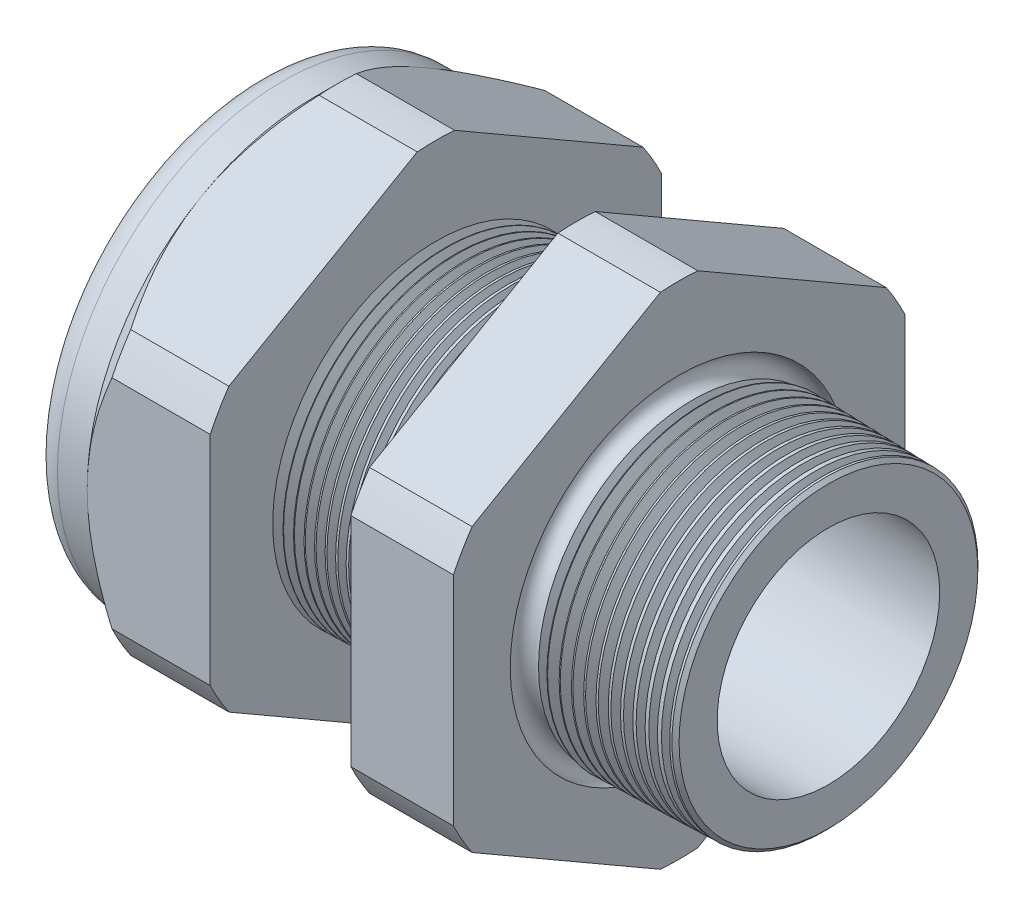
SolidWorks part; units mm, degrees
ref_plane "Front Plane" through (0, 0, 0) normal (0, 0, 1) x (1, 0, 0)
ref_plane "Top Plane" through (0, 0, 0) normal (0, 1, 0) x (1, 0, 0)
ref_plane "Right Plane" through (0, 0, 0) normal (1, 0, 0) x (0, 0, -1)
sketch "Sketch10" plane through (0, 0, 0) normal (0, 0, 1) x (1, 0, 0)
  line L0 (0, 0) -> (-115.3565, 0) construction
  line L1 (-38.862, 9.017) -> (-25.662, 9.017)
  line L2 (3.048, 8.1382) -> (3.048, 11.1862)
  line L3 (-7.874, 11.4722) -> (3.048, 11.1862)
  line L4 (-7.874, 33.02) -> (-7.874, 11.4722)
  line L5 (-7.874, 33.02) -> (-15.374, 33.02)
  line L6 (-15.374, 33.02) -> (-15.374, 11.6686)
  line L7 (-25.662, 11.938) -> (-15.374, 11.6686)
  line L8 (-25.662, 11.938) -> (-25.662, 33.02)
  line L9 (-25.662, 33.02) -> (-34.662, 33.02)
  line L10 (-34.662, 33.02) -> (-34.662, 16.51)
  line L11 (-34.662, 16.51) -> (-38.862, 16.51)
  line L12 (-38.862, 16.51) -> (-38.862, 9.017)
  line L13 (-25.662, 9.017) -> (3.048, 8.1382)
  dimension "D1" = 41.91
  dimension "D2" = 18.034
  dimension "D3" = 1.5
  dimension "D4" = 3.048
  dimension "A" = 23.876
  dimension "D6" = 33.02
  dimension "D8" = 66.04
  dimension "D9" = 4.2
  dimension "D10" = 9
  dimension "D11" = 7.5
  dimension "D" = 10.922
revolve "Revolve2" add sketch "Sketch10" angle 360 about L0
sketch "Sketch12" plane through (-34.662, 0, 0) normal (-1, 0, 0) x (0, 0, 1)
  line L1 (-1.3666, 18.2751) -> (-15.1434, 10.3211)
  line L2 (-16.51, 7.954) -> (-16.51, -7.954)
  line L3 (-15.1434, -10.3211) -> (-1.3666, -18.2751)
  line L4 (1.3666, -18.2751) -> (15.1434, -10.3211)
  line L5 (16.51, -7.954) -> (16.51, 7.954)
  line L6 (15.1434, 10.3211) -> (1.3666, 18.2751)
  circle A0 centre (0, 0) radius 16.51 construction
  arc A1 (1.3666, 18.2751) -> (-1.3666, 18.2751) centre (0, 0) ccw
  arc A2 (-15.1434, 10.3211) -> (-16.51, 7.954) centre (0, 0) ccw
  arc A3 (-16.51, -7.954) -> (-15.1434, -10.3211) centre (0, 0) ccw
  arc A4 (-1.3666, -18.2751) -> (1.3666, -18.2751) centre (0, 0) ccw
  arc A5 (15.1434, -10.3211) -> (16.51, -7.954) centre (0, 0) ccw
  arc A6 (16.51, 7.954) -> (15.1434, 10.3211) centre (0, 0) ccw
  dimension "D2" = 36.6522
  dimension "D1" = 33.02
extrude "Cut-Extrude2" cut sketch "Sketch12" against normal through all flip side to cut
fillet "Fillet4" radius 2.032 1 edges at (-38.862, 0, -16.51)
sketch "Sketch19" plane through (-34.662, 0, 0) normal (-1, 0, 0) x (0, 0, 1)
  line L0 (16.51, 0) -> (16.51, 7.954) construction
  circle A0 centre (0, 0) radius 16.51
extrude "Cut-Extrude3" cut sketch "Sketch19" against normal blind 3.998 draft 45 flip side to cut
chamfer "Chamfer1" distance 0.254 angle 45 1 edges at (3.048, 0, -11.1862)
sketch "Sketch21" plane through (-38.862, 0, 0) normal (-1, 0, 0) x (0, 0, 1)
  circle A0 centre (0, 0) radius 9.017
  circle A2 centre (0, 0) radius 9.017 construction
extrude "plug" add sketch "Sketch21" against normal blind 8.89 separate body
sketch "Sketch22" plane through (-38.862, 0, 0) normal (-1, 0, 0) x (0, 0, 1)
  circle A0 centre (0, 0) radius 8.763
  circle A1 centre (0, 0) radius 9.017 construction
  dimension "D1" = 0.254
extrude "Cut-Extrude4" cut sketch "Sketch22" against normal blind 0.508
sketch "Sketch27" plane through (-38.354, 0, 0) normal (-1, 0, 0) x (0, 0, 1)
  line L0 (-4.3624, 0) -> (4.3624, 0) construction
  circle A0 centre (-4.8103, 0) radius 3.937
  circle A1 centre (0, 0) radius 8.763 construction
  dimension "D1" = 0.0157
  dimension "holedia" = 7.874
extrude "plugholes" cut sketch "Sketch27" against normal through all
pattern_circular "CirPattern1" count 2 over 360 about axis through (0, 0, 0) along (1, 0, 0) of "plugholes"
sketch "Sketch28" [suppressed] plane through (-29.464, 0, 0) normal (-1, 0, 0) x (0, 0, 1)
  circle A0 centre (0, 0) radius 0.762
  dimension "midholedia" = 7.874
extrude "midhole" [suppressed] cut sketch "Sketch28" against normal through all
sketch "Sketch29" plane through (0, 0, 0) normal (0, 0, 1) x (1, 0, 0)
  line L0 (-25.662, 11.938) -> (-24.929, 11.9188)
  line L1 (-15.374, 11.6686) -> (-25.662, 11.938) construction
  line L2 (-24.929, 11.9188) -> (-25.3121, 11.2936)
  line L3 (-25.3121, 11.2936) -> (-25.662, 11.938)
  dimension "D1" = 60
  dimension "D2" = 60
  dimension "D3" = 0.635
revolve "Cut-Revolve1" cut sketch "Sketch29" angle 360 about axis through (0, 0, 0) along (-1, 0, 0)
pattern_linear "LPattern1" count 14 spacing 0.762 along (1, 0, 0) of "Cut-Revolve1"
sketch "Sketch30" plane through (0, 0, 0) normal (0, 0, 1) x (1, 0, 0)
  line L0 (-7.874, 11.4722) -> (-6.9944, 11.4492)
  line L1 (-7.874, 18.2751) -> (-7.874, 10.3211) construction
  line L2 (2.7941, 11.1929) -> (-7.874, 11.4722) construction
  line L3 (-6.9944, 11.4492) -> (-7.4542, 10.6989)
  line L4 (-7.4542, 10.6989) -> (-7.874, 11.4722)
  dimension "D1" = 60
  dimension "D2" = 60
  dimension "D3" = 0.762
revolve "Cut-Revolve2" cut sketch "Sketch30" angle 360 about axis through (0, 0, 0) along (-1, 0, 0)
pattern_linear "LPattern2" count 12 spacing 0.889 along (1, 0, 0) of "Cut-Revolve2"
sketch "Sketch31" [suppressed] plane through (-38.354, 0, 0) normal (-1, 0, 0) x (0, 0, 1)
  line L0 (-1.905, 1.905) -> (1.905, 1.905)
  line L1 (-1.905, -1.905) -> (1.905, -1.905)
  circle A0 centre (0, 0) radius 1.905 construction
  arc A1 (-1.905, 1.905) -> (-1.905, -1.905) centre (-1.905, 0) ccw
  arc A2 (1.905, 1.905) -> (1.905, -1.905) centre (1.905, 0) cw
extrude "Cut-Extrude5" [suppressed] cut sketch "Sketch31" against normal through all
sketch "Sketch32" plane through (0, 0, 0) normal (0, 0, 1) x (1, 0, 0)
  line L0 (-7.874, 18.2751) -> (-7.874, 10.3211) construction
  circle A0 centre (-7.747, 11.4722) radius 0.889
  dimension "D2" = 1.778
  dimension "D1" = 0.127
revolve "Cut-Revolve3" cut sketch "Sketch32" angle 360 about axis through (0, 0, 0) along (-1, 0, 0)
